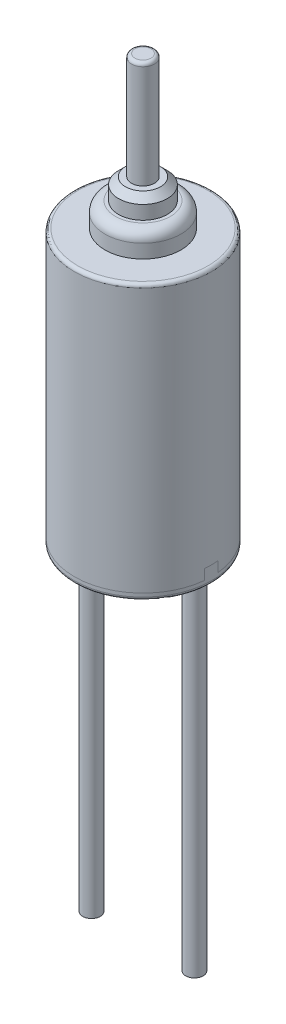
SolidWorks part; units mm, degrees
ref_plane "Front Plane" through (0, 0, 0) normal (0, 0, 1) x (1, 0, 0)
ref_plane "Top Plane" through (0, 0, 0) normal (0, 1, 0) x (1, 0, 0)
ref_plane "Right Plane" through (0, 0, 0) normal (1, 0, 0) x (0, 0, -1)
sketch "Sketch1" plane through (0, 0, 0) normal (0, 1, 0) x (1, 0, 0)
  circle A0 centre (0, 0) radius 2
  dimension "D1" = 4
extrude "Boss-Extrude1" add sketch "Sketch1" along normal blind 8
sketch "Sketch2" plane through (0, 8, 0) normal (0, 1, 0) x (1, 0, 0)
  circle A0 centre (0, 0) radius 1.105
  dimension "D1" = 2.21
extrude "Boss-Extrude2" add sketch "Sketch2" along normal blind 0.7
sketch "Sketch3" plane through (0, 8.7, 0) normal (0, 1, 0) x (1, 0, 0)
  circle A0 centre (0, 0) radius 0.71
  dimension "D1" = 1.42
extrude "Boss-Extrude3" add sketch "Sketch3" along normal blind 0.6 separate body
sketch "Sketch4" plane through (0, 9.3, 0) normal (0, 1, 0) x (1, 0, 0)
  circle A0 centre (0, 0) radius 0.335
  dimension "D1" = 0.67
extrude "Boss-Extrude4" add sketch "Sketch4" along normal blind 3.11 separate body
sketch "Sketch5" plane through (0, 0, 0) normal (1, 0, 0) x (0, 0, -1)
  line L0 (-2, 0.2) -> (-0.2, 0.2)
  line L1 (-2, 8) -> (-2, 0) construction
  line L2 (-0.2, 0.2) -> (-0.2, 0.5)
  line L3 (-0.2, 0.5) -> (0.2, 0.5)
  line L4 (0, 2.2) -> (0, -2.2) construction
  line L5 (0.2, 0.2) -> (0.2, 0.5)
  line L6 (2, 0.2) -> (0.2, 0.2)
  line L7 (2.2, 0) -> (-2.2, 0) construction
  point P10 (0, 0.5)
  dimension "D1" = 0.2
  dimension "D2" = 0.4
  dimension "D3" = 0.3
split "Split1" trim tools "Sketch5" bodies to split 102 resulting bodies 105 106
fillet "Fillet1" radius 0.1 1 edges at (0, 0, 2)
fillet "Fillet2" radius 0.1 1 edges at (0, 8, 2)
fillet "Fillet3" radius 0.3 1 edges at (0, 8.7, 1.105)
chamfer "Chamfer1" distance 0.2 angle 45 1 edges at (0, 9.3, 0.71)
fillet "Fillet4" radius 0.1 1 edges at (0, 12.41, 0.335)
sketch "Sketch6" plane through (0, 0, 0) normal (0, -1, 0) x (1, 0, 0)
  line L0 (0, -2.2) -> (0, 2.2) construction
  circle A0 centre (-1.5, 0) radius 0.255
  circle A1 centre (1.5, 0) radius 0.255
  dimension "D1" = 0.51
  dimension "D2" = 1.5
extrude "Boss-Extrude5" add sketch "Sketch6" along normal blind 10 separate body
